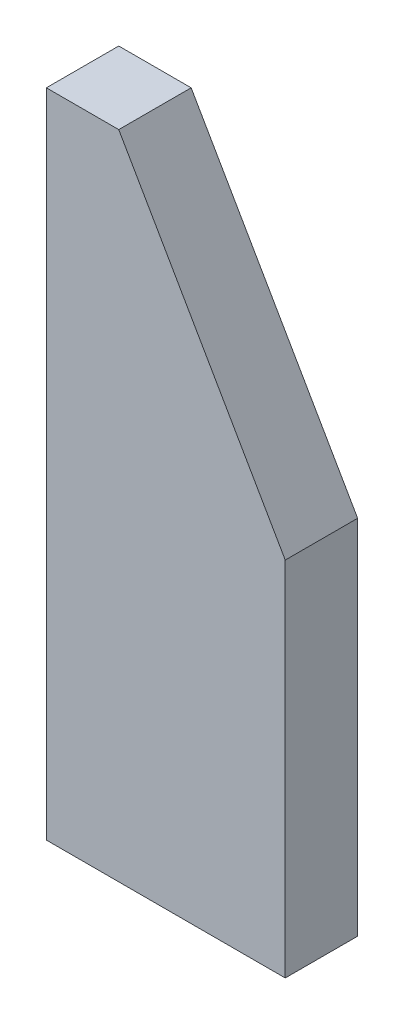
SolidWorks part; units mm, degrees
material "1023 Листовая углеродистая сталь (SS)"
ref_plane "Front" through (0, 0, 0) normal (0, 0, 1) x (1, 0, 0)
ref_plane "Top" through (0, 0, 0) normal (0, 1, 0) x (1, 0, 0)
ref_plane "Right" through (0, 0, 0) normal (1, 0, 0) x (0, 0, -1)
sketch "Sketch1" plane through (0, 0, 0) normal (0, 0, 1) x (1, 0, 0)
  line L0 (0, 0) -> (66, 0)
  line L1 (66, 0) -> (66, 100)
  line L2 (66, 100) -> (20, 180)
  line L3 (20, 180) -> (0, 180)
  line L4 (0, 180) -> (0, 0)
  dimension "D1" = 66
  dimension "D2" = 100
  dimension "D3" = 180
  dimension "D4" = 20
extrude "Extrude1" add sketch "Sketch1" along normal blind 20
